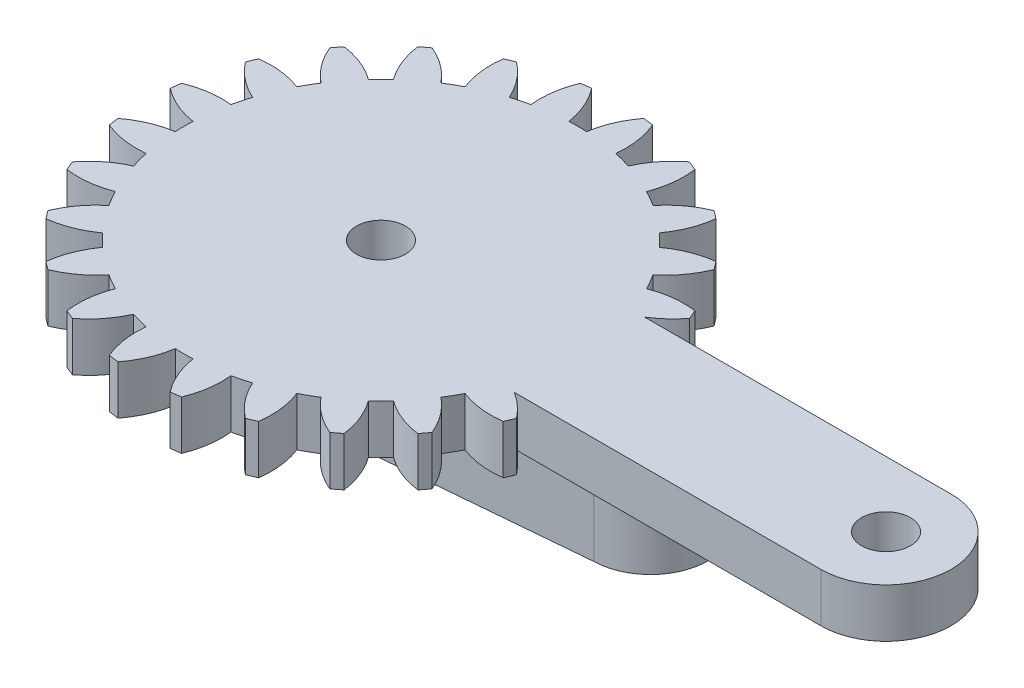
SolidWorks part; units mm, degrees
ref_plane "Front" through (0, 0, 0) normal (0, 0, 1) x (1, 0, 0)
ref_plane "Top" through (0, 0, 0) normal (0, 1, 0) x (1, 0, 0)
ref_plane "Right" through (0, 0, 0) normal (1, 0, 0) x (0, 0, -1)
sketch "Sketch1" plane through (0, 0, 0) normal (0, 1, 0) x (1, 0, 0)
  line L0 (11.068, -3.7704) -> (29.88, -3.7704)
  line L1 (29.88, 4.2296) -> (11.068, 4.2296)
  circle A0 centre (29.88, 0.2296) radius 1.5
  arc A1 (12.5081, -5.0775) -> (11.068, -3.7704) centre (8.218, -8.3571) ccw
  arc A2 (12.2692, -5.6542) -> (12.5081, -5.0775) centre (-1.12, 0.2296) ccw
  arc A3 (9.6134, -5.3407) -> (12.2692, -5.6542) centre (11.5547, -0.3017) ccw
  arc A4 (9.0707, -6.2807) -> (9.6134, -5.3407) centre (-1.12, 0.2296) ccw
  arc A5 (10.6701, -8.4239) -> (9.0707, -6.2807) centre (5.6774, -10.4814) ccw
  arc A6 (10.2901, -8.9191) -> (10.6701, -8.4239) centre (-1.12, 0.2296) ccw
  arc A7 (7.806, -7.9289) -> (10.2901, -8.9191) centre (10.9853, -3.564) ccw
  arc A8 (7.0385, -8.6964) -> (7.806, -7.9289) centre (-1.12, 0.2296) ccw
  arc A9 (8.0287, -11.1806) -> (7.0385, -8.6964) centre (2.6736, -11.8757) ccw
  arc A10 (7.5335, -11.5605) -> (8.0287, -11.1806) centre (-1.12, 0.2296) ccw
  arc A11 (5.3903, -9.9611) -> (7.5335, -11.5605) centre (9.591, -6.5678) ccw
  arc A12 (4.4502, -10.5038) -> (5.3903, -9.9611) centre (-1.12, 0.2296) ccw
  arc A13 (4.7638, -13.1596) -> (4.4502, -10.5038) centre (-0.5887, -12.4451) ccw
  arc A14 (4.1871, -13.3985) -> (4.7638, -13.1596) centre (-1.12, 0.2296) ccw
  arc A15 (2.5309, -11.2988) -> (4.1871, -13.3985) centre (7.4667, -9.1084) ccw
  arc A16 (1.4824, -11.5798) -> (2.5309, -11.2988) centre (-1.12, 0.2296) ccw
  arc A17 (1.0979, -14.2262) -> (1.4824, -11.5798) centre (-3.8873, -12.1507) ccw
  arc A18 (0.4791, -14.3077) -> (1.0979, -14.2262) centre (-1.12, 0.2296) ccw
  arc A19 (-0.5773, -11.851) -> (0.4791, -14.3077) centre (4.7572, -11.0127) ccw
  arc A20 (-1.6627, -11.851) -> (-0.5773, -11.851) centre (-1.12, 0.2296) ccw
  arc A21 (-2.7191, -14.3077) -> (-1.6627, -11.851) centre (-6.9973, -11.0127) ccw
  arc A22 (-3.338, -14.2262) -> (-2.7191, -14.3077) centre (-1.12, 0.2296) ccw
  arc A23 (-3.7225, -11.5798) -> (-3.338, -14.2262) centre (1.6473, -12.1507) ccw
  arc A24 (-4.7709, -11.2988) -> (-3.7225, -11.5798) centre (-1.12, 0.2296) ccw
  arc A25 (-6.4272, -13.3985) -> (-4.7709, -11.2988) centre (-9.7067, -9.1084) ccw
  arc A26 (-7.0038, -13.1596) -> (-6.4272, -13.3985) centre (-1.12, 0.2296) ccw
  arc A27 (-6.6903, -10.5038) -> (-7.0038, -13.1596) centre (-1.6513, -12.4451) ccw
  arc A28 (-7.6303, -9.9611) -> (-6.6903, -10.5038) centre (-1.12, 0.2296) ccw
  arc A29 (-9.7735, -11.5605) -> (-7.6303, -9.9611) centre (-11.831, -6.5678) ccw
  arc A30 (-10.2687, -11.1806) -> (-9.7735, -11.5605) centre (-1.12, 0.2296) ccw
  arc A31 (-9.2785, -8.6964) -> (-10.2687, -11.1806) centre (-4.9137, -11.8757) ccw
  arc A32 (-10.046, -7.9289) -> (-9.2785, -8.6964) centre (-1.12, 0.2296) ccw
  arc A33 (-12.5302, -8.9191) -> (-10.046, -7.9289) centre (-13.2254, -3.564) ccw
  arc A34 (-12.9102, -8.4239) -> (-12.5302, -8.9191) centre (-1.12, 0.2296) ccw
  arc A35 (-11.3107, -6.2807) -> (-12.9102, -8.4239) centre (-7.9175, -10.4814) ccw
  arc A36 (-11.8535, -5.3407) -> (-11.3107, -6.2807) centre (-1.12, 0.2296) ccw
  arc A37 (-14.5093, -5.6542) -> (-11.8535, -5.3407) centre (-13.7947, -0.3017) ccw
  arc A38 (-14.7481, -5.0775) -> (-14.5093, -5.6542) centre (-1.12, 0.2296) ccw
  arc A39 (-12.6485, -3.4213) -> (-14.7481, -5.0775) centre (-10.4581, -8.3571) ccw
  arc A40 (-12.9294, -2.3728) -> (-12.6485, -3.4213) centre (-1.12, 0.2296) ccw
  arc A41 (-15.5759, -1.9883) -> (-12.9294, -2.3728) centre (-13.5004, 2.9969) ccw
  arc A42 (-15.6573, -1.3695) -> (-15.5759, -1.9883) centre (-1.12, 0.2296) ccw
  arc A43 (-13.2006, -0.3131) -> (-15.6573, -1.3695) centre (-12.3623, -5.6476) ccw
  arc A44 (-13.2006, 0.7723) -> (-13.2006, -0.3131) centre (-1.12, 0.2296) ccw
  arc A45 (-15.6573, 1.8287) -> (-13.2006, 0.7723) centre (-12.3623, 6.1069) ccw
  arc A46 (-15.5759, 2.4475) -> (-15.6573, 1.8287) centre (-1.12, 0.2296) ccw
  arc A47 (-12.9294, 2.8321) -> (-15.5759, 2.4475) centre (-13.5004, -2.5377) ccw
  arc A48 (-12.6485, 3.8805) -> (-12.9294, 2.8321) centre (-1.12, 0.2296) ccw
  arc A49 (-14.7481, 5.5368) -> (-12.6485, 3.8805) centre (-10.4581, 8.8163) ccw
  arc A50 (-14.5093, 6.1134) -> (-14.7481, 5.5368) centre (-1.12, 0.2296) ccw
  arc A51 (-11.8535, 5.7999) -> (-14.5093, 6.1134) centre (-13.7947, 0.7609) ccw
  arc A52 (-11.3107, 6.7399) -> (-11.8535, 5.7999) centre (-1.12, 0.2296) ccw
  arc A53 (-12.9102, 8.8831) -> (-11.3107, 6.7399) centre (-7.9175, 10.9406) ccw
  arc A54 (-12.5302, 9.3783) -> (-12.9102, 8.8831) centre (-1.12, 0.2296) ccw
  arc A55 (-10.046, 8.3881) -> (-12.5302, 9.3783) centre (-13.2254, 4.0233) ccw
  arc A56 (-9.2785, 9.1556) -> (-10.046, 8.3881) centre (-1.12, 0.2296) ccw
  arc A57 (-10.2687, 11.6398) -> (-9.2785, 9.1556) centre (-4.9137, 12.3349) ccw
  arc A58 (-9.7735, 12.0198) -> (-10.2687, 11.6398) centre (-1.12, 0.2296) ccw
  arc A59 (-7.6303, 10.4203) -> (-9.7735, 12.0198) centre (-11.831, 7.0271) ccw
  arc A60 (-6.6903, 10.9631) -> (-7.6303, 10.4203) centre (-1.12, 0.2296) ccw
  arc A61 (-7.0038, 13.6188) -> (-6.6903, 10.9631) centre (-1.6513, 12.9043) ccw
  arc A62 (-6.4272, 13.8577) -> (-7.0038, 13.6188) centre (-1.12, 0.2296) ccw
  arc A63 (-4.7709, 11.7581) -> (-6.4272, 13.8577) centre (-9.7067, 9.5677) ccw
  arc A64 (-3.7225, 12.039) -> (-4.7709, 11.7581) centre (-1.12, 0.2296) ccw
  arc A65 (-3.338, 14.6855) -> (-3.7225, 12.039) centre (1.6473, 12.61) ccw
  arc A66 (-2.7191, 14.7669) -> (-3.338, 14.6855) centre (-1.12, 0.2296) ccw
  arc A67 (-1.6627, 12.3102) -> (-2.7191, 14.7669) centre (-6.9973, 11.4719) ccw
  arc A68 (-0.5773, 12.3102) -> (-1.6627, 12.3102) centre (-1.12, 0.2296) ccw
  arc A69 (0.4791, 14.7669) -> (-0.5773, 12.3102) centre (4.7572, 11.4719) ccw
  arc A70 (1.0979, 14.6855) -> (0.4791, 14.7669) centre (-1.12, 0.2296) ccw
  arc A71 (1.4824, 12.039) -> (1.0979, 14.6855) centre (-3.8873, 12.61) ccw
  arc A72 (2.5309, 11.7581) -> (1.4824, 12.039) centre (-1.12, 0.2296) ccw
  arc A73 (4.1871, 13.8577) -> (2.5309, 11.7581) centre (7.4667, 9.5677) ccw
  arc A74 (4.7638, 13.6188) -> (4.1871, 13.8577) centre (-1.12, 0.2296) ccw
  arc A75 (4.4502, 10.9631) -> (4.7638, 13.6188) centre (-0.5887, 12.9043) ccw
  arc A76 (5.3903, 10.4203) -> (4.4502, 10.9631) centre (-1.12, 0.2296) ccw
  arc A77 (7.5335, 12.0198) -> (5.3903, 10.4203) centre (9.591, 7.0271) ccw
  arc A78 (8.0287, 11.6398) -> (7.5335, 12.0198) centre (-1.12, 0.2296) ccw
  arc A79 (7.0385, 9.1556) -> (8.0287, 11.6398) centre (2.6736, 12.3349) ccw
  arc A80 (7.806, 8.3881) -> (7.0385, 9.1556) centre (-1.12, 0.2296) ccw
  arc A81 (10.2901, 9.3783) -> (7.806, 8.3881) centre (10.9853, 4.0233) ccw
  arc A82 (10.6701, 8.8831) -> (10.2901, 9.3783) centre (-1.12, 0.2296) ccw
  arc A83 (9.0707, 6.7399) -> (10.6701, 8.8831) centre (5.6774, 10.9406) ccw
  arc A84 (9.6134, 5.7999) -> (9.0707, 6.7399) centre (-1.12, 0.2296) ccw
  arc A85 (12.2692, 6.1134) -> (9.6134, 5.7999) centre (11.5547, 0.7609) ccw
  arc A86 (12.5081, 5.5368) -> (12.2692, 6.1134) centre (-1.12, 0.2296) ccw
  arc A87 (11.068, 4.2296) -> (12.5081, 5.5368) centre (8.218, 8.8163) ccw
  arc A88 (29.88, -3.7704) -> (29.88, 4.2296) centre (29.88, 0.2296) ccw
  circle A89 centre (-1.12, 0.2296) radius 1.5
extrude "Boss-Extrude1" add sketch "Sketch1" along normal mid plane 3
sketch "Sketch2" plane through (0, -1.5, 0) normal (0, -1, 0) x (1, 0, 0)
  line L0 (-0.3133, 4.715) -> (15.495, 3.3196)
  line L1 (-0.5052, 3.2261) -> (15.42, 1.8204)
  line L3 (15.495, -3.7788) -> (-0.3133, -5.1742)
  line L5 (15.42, -2.2796) -> (-0.5052, -3.6853)
  line L6 (-0.9881, 4.7746) -> (15.495, 3.3196) construction
  line L7 (-1.12, 3.2804) -> (15.42, 1.8204) construction
  line L8 (15.495, -3.7788) -> (-0.9881, -5.2338) construction
  line L9 (15.42, -2.2796) -> (-1.12, -3.7396) construction
  arc A0 (-0.5052, 3.2261) -> (-0.5052, -3.6853) centre (-1.12, -0.2296) ccw
  arc A3 (15.42, -2.2796) -> (15.42, 1.8204) centre (15.42, -0.2296) ccw
  arc A4 (-0.3133, 4.715) -> (-0.3133, -5.1742) centre (-1.12, -0.2296) ccw
  arc A5 (15.495, -3.7788) -> (15.495, 3.3196) centre (15.42, -0.2296) ccw
  arc A6 (-0.2424, 4.7029) -> (-0.2424, -5.1621) centre (-1.12, -0.2296) ccw construction
  dimension "D1" = 1.5
  dimension "D2" = 1.5
extrude "Boss-Extrude2" add sketch "Sketch2" along normal blind 4 contours L0 A5 L3 A4 | L5 A0 L1 A3
